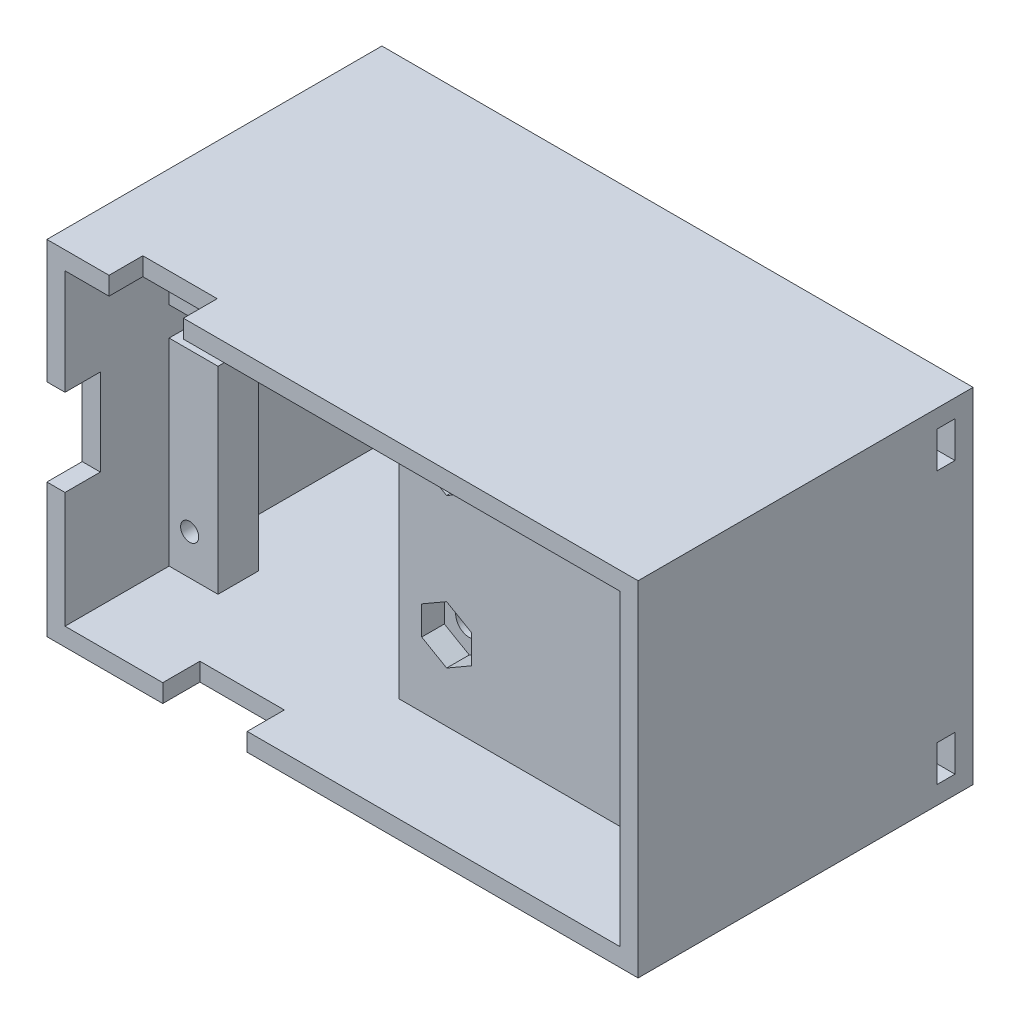
SolidWorks part; units mm, degrees
other "标注1"
sketch "草图16" plane through (3.3763, -43.0665, -26) normal (0.531, -0.7584, -0.3779) x (-0.8474, -0.4776, -0.2321)
other "标注2"
sketch "草图17" plane through (-61.9234, -43.0665, 5.5) normal (-0.5977, -0.3514, 0.7206) x (0.795, -0.3761, 0.4759)
ref_plane "前视基准面" through (0, 0, 0) normal (0, 0, 1) x (1, 0, 0)
ref_plane "上视基准面" through (0, 0, 0) normal (0, 1, 0) x (1, 0, 0)
ref_plane "右视基准面" through (0, 0, 0) normal (1, 0, 0) x (0, 0, -1)
ref_plane "基准面1" through (0, 0, 3.6001) normal (0, 0, 1) x (1, 0, 0)
sketch "草图1" plane through (0, 0, 3.6001) normal (0, 0, 1) x (1, 0, 0)
  line L0 (0.8763, -38.7224) -> (-59.4234, -38.7224) construction
  line L1 (-48.7034, -33.8618) -> (-39.801, -33.8618)
  line L2 (-48.7034, -33.8618) -> (-48.7034, -38.7224)
  line L4 (-39.801, -33.8618) -> (-39.801, -38.7224)
  line L5 (-59.4234, -9.4107) -> (0.8763, -9.4107) construction
  line L7 (-55.7687, -9.4107) -> (-55.7687, -14.2907)
  line L8 (-55.7687, -14.2907) -> (-45.8066, -14.2907)
  line L9 (-45.8066, -9.4107) -> (-45.8066, -14.2907)
  line L10 (-12.699, -17.609) -> (-12.699, -12.109) construction
  line L11 (0.8763, -9.4107) -> (-45.8066, -9.4107)
  line L12 (0.8763, -9.4107) -> (0.8763, -38.7224)
  line L13 (0.8763, -38.7224) -> (-39.801, -38.7224)
  line L14 (-59.4234, -9.4107) -> (-59.4234, -19.2521)
  line L15 (-29.2736, -33.0846) -> (-20.6538, -33.0846)
  line L16 (-29.2736, -33.0846) -> (-29.2736, -36.2921)
  line L17 (-29.2736, -36.2921) -> (-20.6538, -36.2921)
  line L18 (-20.6538, -33.0846) -> (-20.6538, -36.2921)
  line L23 (-12.699, -12.109) -> (-9.399, -12.109)
  line L24 (-12.699, -12.109) -> (-12.699, -17.609)
  line L25 (-12.699, -17.609) -> (-9.399, -17.609)
  line L26 (-9.399, -12.109) -> (-9.399, -17.609)
  line L27 (-48.7034, -38.7224) -> (-59.4234, -38.7224)
  line L28 (-55.7687, -9.4107) -> (-59.4234, -9.4107)
  line L29 (-59.4234, -27.6866) -> (-59.4234, -38.7224)
  line L30 (-59.4234, -19.2521) -> (-54.3557, -19.2521)
  line L32 (-59.4234, -27.6866) -> (-54.3557, -27.6866)
  line L33 (-54.3557, -19.2521) -> (-54.3557, -27.6866)
  circle A0 centre (-57.6581, -36.6498) radius 1
  circle A1 centre (-57.6581, -11.2498) radius 1
  circle A2 centre (-1.016, -11.2498) radius 1
  circle A3 centre (-0.889, -36.8301) radius 1
  circle A4 centre (-4.1259, -29.4689) radius 1.322
  circle A5 centre (-5.9082, -27.2775) radius 0.4462
  circle A6 centre (-4.5737, -26.6799) radius 0.4462
  circle A7 centre (-3.1192, -26.8297) radius 0.4462
  circle A8 centre (-1.9345, -27.6866) radius 0.4462
  circle A9 centre (-1.3369, -29.0211) radius 0.4462
  circle A10 centre (-1.4866, -30.4756) radius 0.4462
  circle A11 centre (-2.3435, -31.6603) radius 0.4462
  circle A12 centre (-3.678, -32.2579) radius 0.4462
  circle A13 centre (-5.1325, -32.1082) radius 0.4462
  circle A14 centre (-6.3173, -31.2513) radius 0.4462
  circle A15 centre (-6.9149, -29.9168) radius 0.4462
  circle A16 centre (-6.7652, -28.4623) radius 0.4462
  point P71 (-4.1259, -29.4689)
  dimension "D1" = 12
ref_plane "基准面2" through (0, 0, -6) normal (0, 0, -1) x (-1, 0, 0)
sketch "草图2" plane through (0, 0, -6) normal (0, 0, -1) x (-1, 0, 0)
  line L0 (29.2736, -9.4107) -> (29.2736, -38.7224) construction
  line L1 (-0.8763, -38.7224) -> (59.4234, -38.7224)
  line L2 (-0.8763, -38.7224) -> (-0.8763, -9.4107)
  line L3 (-0.8763, -9.4107) -> (59.4234, -9.4107)
  line L4 (59.4234, -38.7224) -> (59.4234, -9.4107)
  line L5 (59.4234, -24.0665) -> (-9.3078, -24.0665) construction
  line L6 (-3.3763, -5.0665) -> (61.9234, -43.0665) construction
  line L9 (29.2736, -15.8165) -> (29.2736, -13.1836) construction
  line L10 (27.7854, -15.8165) -> (27.7854, -13.1836)
  line L11 (30.7617, -15.8165) -> (30.7617, -13.1836)
  line L12 (29.2736, -38.7224) -> (29.2736, -43.3487) construction
  line L13 (-3.3763, -43.0665) -> (61.9234, -5.0665) construction
  line L14 (-3.3763, -5.0665) -> (61.9234, -5.0665)
  line L15 (-3.3763, -5.0665) -> (-3.3763, -43.0665)
  line L16 (-3.3763, -43.0665) -> (61.9234, -43.0665)
  line L17 (61.9234, -5.0665) -> (61.9234, -43.0665)
  circle A0 centre (1.016, -11.2498) radius 1
  circle A1 centre (0.889, -36.8301) radius 1
  circle A2 centre (57.6581, -36.6498) radius 1
  circle A3 centre (57.6581, -11.2498) radius 0.9222
  arc A10 (27.7854, -15.8165) -> (30.7617, -15.8165) centre (29.2736, -15.8165) ccw
  arc A11 (30.7617, -13.1836) -> (27.7854, -13.1836) centre (29.2736, -13.1836) ccw
  circle A12 centre (29.2736, -32.3165) radius 1.5
  point P24 (29.2736, -24.0665)
  point P27 (29.2736, -31.5665)
  point P28 (29.2736, -24.0665)
  point P33 (29.2736, -14.5001)
  dimension "D1" = 38
  dimension "D2" = 2.5
  dimension "D3" = 3
  dimension "D4" = 8.25
  dimension "D5" = 2.5
  dimension "D7" = 8.25
extrude "凸台-拉伸2" add sketch "草图2" along normal blind 4.5 separate body
sketch "草图3" plane through (0, 0, -6) normal (0, 0, -1) x (-1, 0, 0)
  line L0 (29.2736, -15.8165) -> (29.2736, -10.8487) construction
  line L1 (32.0236, -17.4043) -> (32.0236, -14.2288)
  line L4 (26.5236, -14.2288) -> (26.5236, -17.4043)
  line L5 (26.5236, -17.4043) -> (29.2736, -18.992)
  line L6 (29.2736, -18.992) -> (32.0236, -17.4043)
  line L8 (32.0236, -14.9203) -> (32.0236, -11.7449)
  line L9 (32.0236, -11.7449) -> (29.2736, -10.1572)
  line L10 (29.2736, -10.1572) -> (26.5236, -11.7449)
  line L11 (26.5236, -11.7449) -> (26.5236, -14.9203)
  line L14 (31.8974, -14.9932) -> (32.0236, -14.9203) [skipped]
  line L15 (29.2736, -22.4541) -> (17.663, -22.4541) construction
  line L16 (29.2736, -22.4541) -> (29.2736, -17.3047) construction
  line L17 (26.6497, -14.156) -> (26.5236, -14.2288) [skipped]
  line L18 (26.5236, -14.9203) -> (26.6497, -14.9932) [skipped]
  line L19 (32.0236, -14.2288) -> (31.8974, -14.156) [skipped]
  line L20 (26.5236, -33.9043) -> (29.2736, -35.492)
  line L21 (29.2736, -35.492) -> (32.0236, -33.9043)
  line L22 (32.0236, -33.9043) -> (32.0236, -30.7288)
  line L23 (32.0236, -30.7288) -> (29.2736, -29.1411)
  line L24 (29.2736, -29.1411) -> (26.5236, -30.7288)
  line L25 (26.5236, -30.7288) -> (26.5236, -33.9043)
  arc A0 (26.82, -14.5746) -> (31.7271, -14.5746) centre (29.2736, -15.8165) ccw construction
  arc A1 (31.7271, -14.5746) -> (26.82, -14.5746) centre (29.2736, -13.3326) ccw construction
  circle A2 centre (29.2736, -32.3165) radius 2.75 construction
  circle A3 centre (1.016, -11.2498) radius 1.75
  circle A4 centre (57.6581, -11.2498) radius 1.75
  arc A5 (27.7854, -15.8165) -> (30.7617, -15.8165) centre (29.2736, -15.8165) ccw construction
  circle A6 centre (0.889, -36.8301) radius 1.75
  circle A7 centre (57.6581, -36.6498) radius 1.75
  point P25 (29.2736, -33.8241)
  dimension "D2" = 3.5
  dimension "D1" = 5.5
extrude "切除-拉伸2" cut sketch "草图3" along normal blind 2.5 contours L10 L11 L4 L5 L6 L1 L8 L9 | L24 L25 L20 L21 L22 L23
sketch "草图5" plane through (0, 0, -10.5) normal (0, 0, -1) x (-1, 0, 0)
  line L0 (29.2736, -7.0665) -> (29.2736, -48.0798) construction
  line L5 (-1.3763, -7.0665) -> (59.9234, -7.0665)
  line L6 (-1.3763, -7.0665) -> (-1.3763, -41.0665)
  line L7 (-1.3763, -41.0665) -> (59.9234, -41.0665)
  line L8 (59.9234, -7.0665) -> (59.9234, -41.0665)
  line L9 (-3.3763, -5.0665) -> (61.9234, -5.0665)
  line L10 (-3.3763, -5.0665) -> (-3.3763, -43.0665)
  line L11 (-3.3763, -43.0665) -> (61.9234, -43.0665)
  line L12 (61.9234, -5.0665) -> (61.9234, -43.0665)
  line L13 (-0.8763, -9.4107) -> (59.4234, -38.7224) construction
  line L14 (-1.3763, -7.0665) -> (59.9234, -41.0665) construction
  line L15 (-3.3763, -5.0665) -> (61.9234, -43.0665) construction
  line L16 (61.9234, -5.0665) -> (-3.3763, -43.0665) construction
  point P12 (29.2736, -24.0665)
  point P13 (29.2736, -24.0665)
  point P18 (29.2736, -24.0665)
  dimension "D1" = 61.2997
  dimension "D2" = 38
  dimension "D3" = 34
  dimension "D4" = 2
extrude "凸台-拉伸3" add sketch "草图5" along normal blind 21 and the other way blind 16
sketch "草图7" plane through (0, -5.0665, 0) normal (0, 1, 0) x (1, 0, 0)
  line L0 (-41.7981, -5.5601) -> (-46.8481, -5.5601) construction
  line L1 (-55.0622, -1.765) -> (-46.8481, -1.765)
  line L2 (-55.0622, -1.765) -> (-55.0622, -5.5601)
  line L3 (-55.0622, -5.5601) -> (-46.8481, -5.5601)
  line L4 (-46.8481, -1.765) -> (-46.8481, -5.5601)
extrude "切除-拉伸4" cut sketch "草图7" against normal blind 3
sketch "草图8" plane through (-61.9234, 0, 0) normal (-1, 0, 0) x (0, 0, 1)
  line L0 (5.6001, -27.6866) -> (5.6001, -38.7224) construction
  line L1 (1.6001, -18.6953) -> (5.6001, -18.6953)
  line L2 (1.6001, -18.6953) -> (1.6001, -28.2708)
  line L3 (1.6001, -28.2708) -> (5.6001, -28.2708)
  line L4 (5.6001, -18.6953) -> (5.6001, -28.2708)
  dimension "D1" = 4
extrude "切除-拉伸5" cut sketch "草图8" against normal blind 3
sketch "草图9" plane through (0, -43.0665, 0) normal (0, -1, 0) x (1, 0, 0)
  line L0 (-59.4234, 5.6001) -> (-48.7034, 5.6001) construction
  line L1 (-49.1273, 5.6001) -> (-39.801, 5.6001)
  line L2 (-49.1273, 5.6001) -> (-49.1273, 1.3978)
  line L3 (-49.1273, 1.3978) -> (-39.801, 1.3978)
  line L4 (-39.801, 5.6001) -> (-39.801, 1.3978)
extrude "切除-拉伸6" cut sketch "草图9" against normal blind 3
sketch "草图13" plane through (0, 0, -6) normal (0, 0, 1) x (1, 0, 0)
  line L2 (-59.9234, -16.0665) -> (-59.9234, -19.2521)
  line L3 (-59.9234, -19.2521) -> (-54.5253, -19.2521)
  line L5 (-59.9234, -16.0665) -> (-54.5253, -16.0665)
  line L6 (-49.1273, -41.0665) -> (-59.9234, -41.0665) construction
  line L7 (-54.5253, -41.0665) -> (-34.5253, -41.0665)
  line L8 (-54.5253, -41.0665) -> (-54.5253, -19.2521)
  line L9 (-54.5253, -7.0665) -> (-34.5253, -7.0665)
  line L10 (-34.5253, -41.0665) -> (-34.5253, -7.0665)
  line L11 (-46.8481, -7.0665) -> (1.3763, -7.0665) construction
  line L12 (-54.5253, -16.0665) -> (-54.5253, -12.8809)
  line L13 (-54.5253, -12.8809) -> (-54.5253, -7.0665)
  dimension "D2" = 20
extrude "切除-拉伸7" cut sketch "草图13" against normal blind 10
sketch "草图15" plane through (0, 0, -10.5) normal (0, 0, -1) x (-1, 0, 0)
  circle A0 centre (1.016, -11.2498) radius 1.75
  circle A1 centre (57.6581, -11.2498) radius 1.75
  circle A2 centre (0.889, -36.8301) radius 1.75
  circle A3 centre (57.6581, -36.6498) radius 1.75
  dimension "D1" = 3.5
extrude "切除-拉伸8" cut sketch "草图15" against normal blind 1.5
sketch "草图18" plane through (0, 0, -31.5) normal (0, 0, -1) x (-1, 0, 0)
  line L0 (59.9234, -7.0665) -> (-1.3763, -7.0665) construction
  line L1 (-1.3763, -6.5665) -> (59.9234, -6.5665)
  line L2 (-1.3763, -6.5665) -> (-1.3763, -41.5665)
  line L3 (-1.3763, -41.5665) -> (59.9234, -41.5665)
  line L4 (59.9234, -6.5665) -> (59.9234, -41.5665)
  line L5 (-1.3763, -41.0665) -> (34.5253, -41.0665) construction
  dimension "D1" = 0.5
  dimension "D2" = 0.5
extrude "切除-拉伸9" cut sketch "草图18" against normal blind 2
sketch "草图19" plane through (1.3763, 0, 0) normal (-1, 0, 0) x (0, 0, 1)
  line L0 (-31.5, -43.0665) -> (-31.5, -5.0665) construction
  line L1 (-29.5, -7.0665) -> (-27.5, -7.0665)
  line L2 (-29.5, -7.0665) -> (-29.5, -11.0665)
  line L3 (-29.5, -11.0665) -> (-27.5, -11.0665)
  line L4 (-27.5, -7.0665) -> (-27.5, -11.0665)
  line L5 (-31.5, -5.0665) -> (5.5, -5.0665) construction
  line L6 (-31.5, -24.0665) -> (15.6063, -24.0665) construction
  line L7 (-29.5, -37.0665) -> (-27.5, -37.0665)
  line L8 (-27.5, -41.0665) -> (-27.5, -37.0665)
  line L9 (-29.5, -41.0665) -> (-27.5, -41.0665)
  line L10 (-29.5, -41.0665) -> (-29.5, -37.0665)
  dimension "D1" = 2
  dimension "D2" = 2
  dimension "D3" = 2
  dimension "D4" = 4
extrude "切除-拉伸10" cut sketch "草图19" against normal blind 2
sketch "草图20" plane through (0, 0, -31.5) normal (0, 0, -1) x (-1, 0, 0)
  line L0 (-1.3763, -24.0665) -> (97.3122, -24.0665) construction
  line L1 (-1.3763, -6.5665) -> (-1.3763, -41.5665) construction
  line L2 (59.9234, -41.5665) -> (59.9234, -6.5665) construction
  line L3 (59.9234, -20.0665) -> (61.9234, -20.0665)
  line L4 (59.9234, -20.0665) -> (59.9234, -28.0665)
  line L5 (59.9234, -28.0665) -> (61.9234, -28.0665)
  line L6 (61.9234, -20.0665) -> (61.9234, -28.0665)
  line L7 (61.9234, -43.0665) -> (61.9234, -5.0665) construction
  line L8 (59.9234, -20.0665) -> (61.9234, -28.0665) construction
  line L9 (61.9234, -20.0665) -> (59.9234, -28.0665) construction
  point P12 (60.9234, -24.0665)
  dimension "D1" = 8
extrude "切除-拉伸11" cut sketch "草图20" against normal blind 1.2
sketch "草图21" plane through (-61.9234, 0, 0) normal (-1, 0, 0) x (0, 0, 1)
  line L0 (-30.3, -20.0665) -> (-31.5, -20.0665) construction
  line L1 (-28.7, -20.0665) -> (-26.7, -20.0665)
  line L2 (-28.7, -20.0665) -> (-28.7, -28.0665)
  line L3 (-28.7, -28.0665) -> (-26.7, -28.0665)
  line L4 (-26.7, -20.0665) -> (-26.7, -28.0665)
  line L5 (-30.3, -28.0665) -> (-31.5, -28.0665) construction
  line L6 (-30.3, -28.0665) -> (-30.3, -20.0665) construction
  dimension "D1" = 2
  dimension "D2" = 1.6
extrude "切除-拉伸12" cut sketch "草图21" against normal blind 2
